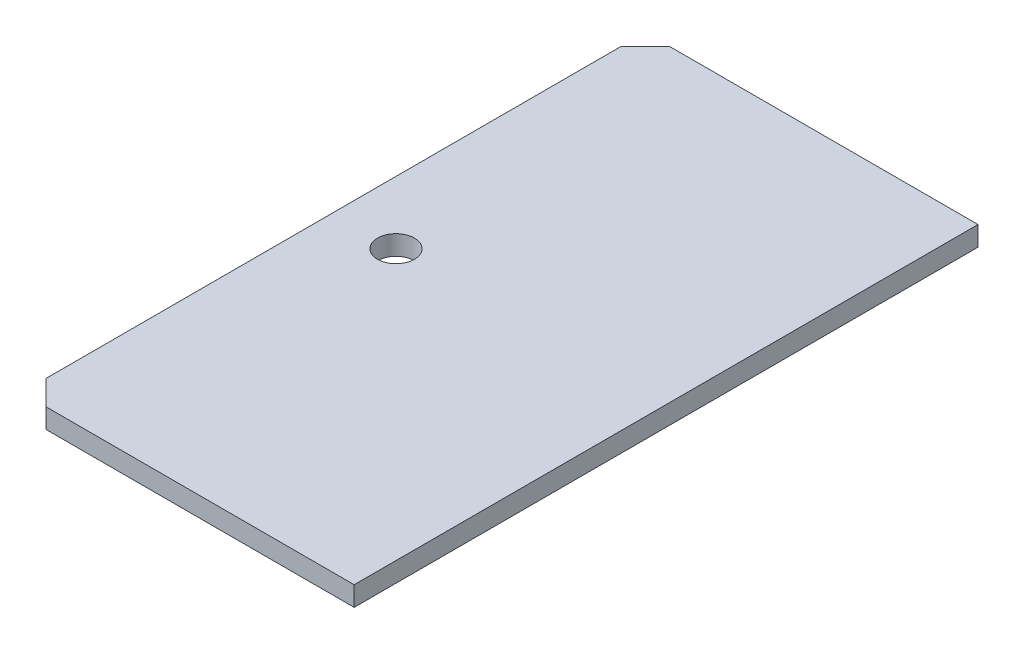
SolidWorks part; units mm, degrees
ref_plane "Front Plane" through (0, 0, 0) normal (0, 0, 1) x (1, 0, 0)
ref_plane "Top Plane" through (0, 0, 0) normal (0, 1, 0) x (1, 0, 0)
ref_plane "Right Plane" through (0, 0, 0) normal (1, 0, 0) x (0, 0, -1)
sketch "Sketch1" plane through (0, 0, 0) normal (0, 1, 0) x (1, 0, 0)
  line L1 (-40.64, 25.4) -> (40.64, 25.4)
  line L2 (-40.64, 25.4) -> (-40.64, -25.4)
  line L3 (-40.64, -25.4) -> (40.64, -25.4)
  line L4 (40.64, 25.4) -> (40.64, -25.4)
  line L5 (-40.64, 25.4) -> (40.64, -25.4) construction
  line L6 (-40.64, -25.4) -> (40.64, 25.4) construction
  point P0 (0, 0)
  dimension "D1" = 81.28
  dimension "D2" = 50.8
extrude "Boss-Extrude1" add sketch "Sketch1" along normal blind 1.6002
sketch "Sketch2" plane through (0, 1.6002, 0) normal (0, 1, 0) x (1, 0, 0)
  line L0 (-40.64, 0) -> (-35.54, 0) construction
  line L1 (-40.64, 25.4) -> (-40.64, -25.4) construction
  circle A0 centre (-35.54, 0) radius 1.5
  circle A2 centre (35.56, 0) radius 1.5
  circle A3 centre (0, 0) radius 1.5
  dimension "D1" = 71.1
  dimension "D3" = 3
  dimension "D4" = 3
  dimension "D5" = 3
  dimension "D2" = 5.1
  dimension "D6" = 35.56
extrude "Cut-Extrude1" cut sketch "Sketch2" against normal blind 1.6002
chamfer "Chamfer1" distance 2 angle 45 4 edges at (40.64, 0.8001, 25.4) (-40.64, 0.8001, 25.4) (-40.64, 0.8001, -25.4) (40.64, 0.8001, -25.4)
sketch "Sketch3" plane through (0, 0, 0) normal (0, -1, 0) x (1, 0, 0)
  line L0 (-40.64, 0) -> (-13.5467, 0) construction
  line L1 (-40.64, -23.4) -> (-40.64, 23.4) construction
  line L2 (-13.5467, 25.4) -> (-13.5467, -25.4)
  line L3 (-38.64, 25.4) -> (38.64, 25.4) construction
  line L4 (38.64, -25.4) -> (-38.64, -25.4) construction
  line L5 (-13.5467, 25.4) -> (38.64, 25.4)
  line L6 (38.64, 25.4) -> (40.64, 23.4)
  line L7 (40.64, 23.4) -> (40.64, -23.4)
  line L8 (40.64, -23.4) -> (38.64, -25.4)
  line L9 (38.64, -25.4) -> (-13.5467, -25.4)
  dimension "D1" = 27.0933
extrude "Cut-Extrude2" cut sketch "Sketch3" against normal blind 10
